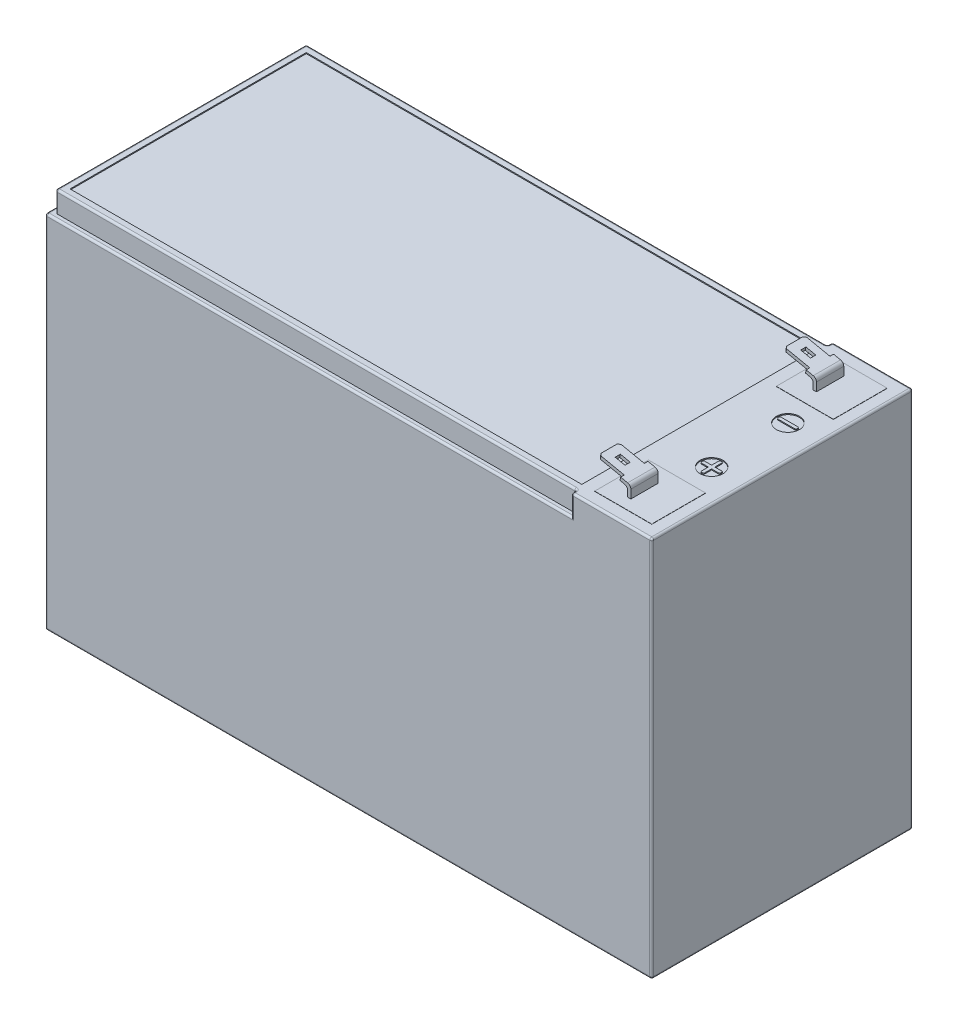
SolidWorks part; units mm, degrees
ref_plane "Front Plane" through (0, 0, 0) normal (0, 0, 1) x (1, 0, 0)
ref_plane "Top Plane" through (0, 0, 0) normal (0, 1, 0) x (1, 0, 0)
ref_plane "Right Plane" through (0, 0, 0) normal (1, 0, 0) x (0, 0, -1)
sketch "Sketch1" plane through (0, 0, 0) normal (0, 1, 0) x (1, 0, 0)
  line L1 (-75.0564, 43.5611) -> (75.9436, 43.5611)
  line L2 (-75.0564, 43.5611) -> (-75.0564, -21.4389)
  line L3 (-75.0564, -21.4389) -> (75.9436, -21.4389)
  line L4 (75.9436, 43.5611) -> (75.9436, -21.4389)
  dimension "D1" = 151
  dimension "D2" = 65
extrude "Boss-Extrude1" add sketch "Sketch1" along normal blind 95
ref_plane "Plane1" through (0, 0, 15.4389) normal (0, 0, 1) x (1, 0, 0)
sketch "Sketch2" plane through (0, 0, 15.4389) normal (0, 0, 1) x (1, 0, 0)
  line L0 (63.9436, 95) -> (63.9436, 97.3257)
  line L1 (-75.0564, 95) -> (75.9436, 95) construction
  line L2 (63.9436, 97.3257) -> (55.7698, 99.03)
  line L3 (55.7698, 99.03) -> (55.9331, 99.8131)
  line L4 (55.9331, 99.8131) -> (64.7436, 97.9761)
  line L5 (64.7436, 97.9761) -> (64.7436, 95)
  line L6 (64.7436, 95) -> (63.9436, 95)
  line L7 (75.9436, 95) -> (75.9436, 0) construction
  point P10 (0, 0)
  dimension "D1" = 12
  dimension "D2" = 9
  dimension "D3" = 0.8
  dimension "D4" = 0.8
extrude "Boss-Extrude2" add sketch "Sketch2" against normal blind 6.8
ref_plane "Plane2" through (0, 0, -11.0611) normal (0, 0, 1) x (1, 0, 0)
sketch "Sketch4" plane through (22.274, 106.8309, 0) normal (0.2041, 0.9789, 0) x (0.9789, -0.2041, 0)
  line L0 (40.7829, -8.6389) -> (40.7829, -9.5389)
  line L1 (43.3829, -8.6389) -> (34.3829, -8.6389) construction
  line L2 (40.7829, -9.5389) -> (34.3829, -9.5389)
  line L3 (34.3829, -8.6389) -> (34.3829, -15.4389) construction
  line L4 (34.3829, -9.5389) -> (34.3829, -8.6389)
  line L5 (34.3829, -8.6389) -> (40.7829, -8.6389)
  line L6 (40.7829, -14.5389) -> (40.7829, -15.4389)
  line L7 (-52.25, -15.4389) -> (52.25, -15.4389) construction
  line L8 (40.7829, -14.5389) -> (34.3829, -14.5389)
  line L9 (34.3829, -14.5389) -> (34.3829, -15.4389)
  line L10 (34.3829, -15.4389) -> (40.7829, -15.4389)
  line L12 (36.5829, -11.3889) -> (39.0829, -11.3889)
  line L13 (36.5829, -11.3889) -> (36.5829, -12.6889)
  line L14 (36.5829, -12.6889) -> (39.0829, -12.6889)
  line L15 (39.0829, -11.3889) -> (39.0829, -12.6889)
  dimension "D1" = 0.9
  dimension "D2" = 0.9
  dimension "D3" = 6.4
  dimension "D4" = 2.2
  dimension "D5" = 2.5
  dimension "D6" = 1.3
  dimension "D7" = 1.85
  dimension "D8" = 1.85
extrude "Cut-Extrude1" cut sketch "Sketch4" against normal up to next (0.8 mm away)
chamfer "Chamfer1" distance 0.5 angle 45 2 edges at (55.8514, 99.4215, 9.5389) (55.8514, 99.4215, 14.5389)
fillet "Fillet1" radius 1 2 edges at (63.9436, 97.3257, 12.0389) (64.7436, 97.9761, 12.0389)
mirror "Mirror1" about plane through (0, 0, -11.0611) normal (0, 0, 1) of "Fillet1", "Chamfer1", "Cut-Extrude1", "Boss-Extrude2"
sketch "Sketch5" plane through (0, 95, 0) normal (0, 1, 0) x (1, 0, 0)
  line L0 (55.9436, -21.4389) -> (55.9436, -20.1389)
  line L1 (-75.0564, -21.4389) -> (75.9436, -21.4389) construction
  line L2 (55.9436, -20.1389) -> (-73.7564, -20.1389)
  line L3 (-73.7564, -20.1389) -> (-73.7564, 42.2611)
  line L4 (-73.7564, 42.2611) -> (55.9436, 42.2611)
  line L5 (55.9436, 42.2611) -> (55.9436, 43.5611)
  line L6 (75.9436, 43.5611) -> (-75.0564, 43.5611) construction
  line L7 (55.9436, 43.5611) -> (-75.0564, 43.5611)
  line L8 (-75.0564, 43.5611) -> (-75.0564, -21.4389)
  line L9 (-75.0564, -21.4389) -> (55.9436, -21.4389)
  line L10 (75.9436, -21.4389) -> (75.9436, 43.5611) construction
  dimension "D1" = 1.3
  dimension "D2" = 1.3
  dimension "D3" = 1.3
  dimension "D4" = 20
  dimension "D5" = 20
extrude "Cut-Extrude2" cut sketch "Sketch5" against normal blind 5.2
fillet "Fillet2" radius 0.5 25 edges at (0.4436, 0, -43.5611) (-75.0564, 44.9, -43.5611) (-75.0564, 0, -11.0611) (-75.0564, 44.9, 21.4389) (75.9436, 0, -11.0611) (0.4436, 0, 21.4389) (75.9436, 47.5, -43.5611) (65.9436, 95, -43.5611) (55.9436, 92.4, -43.5611) (55.9436, 92.4, -42.2611) (55.9436, 95, -42.9111) (-9.5564, 89.8, -43.5611) (-8.9064, 95, -42.2611) (-73.7564, 92.4, -42.2611) (-73.7564, 92.4, 20.1389) (-75.0564, 89.8, -11.0611) (55.9436, 92.4, 20.1389) (-9.5564, 89.8, 21.4389) (55.9436, 92.4, 21.4389) (75.9436, 47.5, 21.4389) (75.9436, 95, -11.0611) (65.9436, 95, 21.4389) (55.9436, 95, 20.7889) (-8.9064, 95, 20.1389) (-73.7564, 95, -11.0611)
sketch "Sketch6" plane through (0, 95, 0) normal (0, 1, 0) x (1, 0, 0)
  line L0 (-73.7564, -19.6389) -> (-73.7564, 41.7611) construction
  line L1 (-71.9564, 40.4611) -> (55.4436, 40.4611)
  line L2 (-71.9564, 40.4611) -> (-71.9564, -18.3389)
  line L3 (-71.9564, -18.3389) -> (55.4436, -18.3389)
  line L4 (55.4436, 40.4611) -> (55.4436, -18.3389)
  line L5 (-73.2564, 42.2611) -> (55.4436, 42.2611) construction
  line L6 (55.4436, -20.1389) -> (-73.2564, -20.1389) construction
  line L7 (75.9436, 43.0611) -> (75.9436, -20.9389) construction
  line L8 (56.4436, 43.5611) -> (75.4436, 43.5611) construction
  line L9 (75.4436, -21.4389) -> (56.4436, -21.4389) construction
  line L10 (67.4436, 3.7111) -> (67.4436, 1.9611)
  line L11 (65.6936, 20.9611) -> (69.9936, 20.9611)
  line L12 (65.4436, 20.7111) -> (65.4436, 20.4111)
  line L13 (65.6936, 20.1611) -> (69.9936, 20.1611)
  line L14 (70.2436, 20.7111) -> (70.2436, 20.4111)
  line L15 (67.4436, 1.9611) -> (65.6936, 1.9611)
  line L16 (65.4436, 1.7111) -> (65.4436, 1.4111)
  line L17 (65.6936, 1.1611) -> (67.4436, 1.1611)
  line L18 (67.4436, 1.1611) -> (67.4436, -0.5889)
  line L19 (67.6936, -0.8389) -> (67.9936, -0.8389)
  line L20 (68.2436, -0.5889) -> (68.2436, 1.1611)
  line L21 (68.2436, 1.1611) -> (69.9936, 1.1611)
  line L22 (70.2436, 1.4111) -> (70.2436, 1.7111)
  line L23 (69.9936, 1.9611) -> (68.2436, 1.9611)
  line L24 (68.2436, 1.9611) -> (68.2436, 3.7111)
  line L25 (67.9936, 3.9611) -> (67.6936, 3.9611)
  line L27 (72.7436, 40.3611) -> (58.5436, 40.3611)
  line L28 (72.7436, 40.3611) -> (72.7436, 26.9611)
  line L29 (72.7436, 26.9611) -> (58.5436, 26.9611)
  line L30 (58.5436, 40.3611) -> (58.5436, 26.9611)
  line L31 (72.7436, -18.2389) -> (58.5436, -18.2389)
  line L32 (72.7436, -18.2389) -> (72.7436, -4.8389)
  line L33 (72.7436, -4.8389) -> (58.5436, -4.8389)
  line L34 (58.5436, -18.2389) -> (58.5436, -4.8389)
  circle A0 centre (67.8436, 20.5611) radius 2.875
  circle A1 centre (67.8436, 1.5611) radius 2.875
  arc A2 (69.9936, 20.1611) -> (70.2436, 20.4111) centre (69.9936, 20.4111) ccw
  arc A3 (70.2436, 20.7111) -> (69.9936, 20.9611) centre (69.9936, 20.7111) ccw
  arc A4 (65.6936, 20.1611) -> (65.4436, 20.4111) centre (65.6936, 20.4111) cw
  arc A5 (65.6936, 20.9611) -> (65.4436, 20.7111) centre (65.6936, 20.7111) ccw
  arc A6 (65.6936, 1.1611) -> (65.4436, 1.4111) centre (65.6936, 1.4111) cw
  arc A7 (65.4436, 1.7111) -> (65.6936, 1.9611) centre (65.6936, 1.7111) cw
  arc A8 (67.6936, -0.8389) -> (67.4436, -0.5889) centre (67.6936, -0.5889) cw
  arc A9 (67.9936, -0.8389) -> (68.2436, -0.5889) centre (67.9936, -0.5889) ccw
  arc A10 (69.9936, 1.1611) -> (70.2436, 1.4111) centre (69.9936, 1.4111) ccw
  arc A11 (70.2436, 1.7111) -> (69.9936, 1.9611) centre (69.9936, 1.7111) ccw
  arc A12 (68.2436, 3.7111) -> (67.9936, 3.9611) centre (67.9936, 3.7111) ccw
  arc A13 (67.6936, 3.9611) -> (67.4436, 3.7111) centre (67.6936, 3.7111) ccw
  dimension "D5" = 5.75
  dimension "D8" = 5.75
  dimension "D27" = 0.25
  dimension "D1" = 1.8
  dimension "D2" = 1.8
  dimension "D3" = 1.8
  dimension "D4" = 20.5
  dimension "D6" = 8.1
  dimension "D7" = 23
  dimension "D9" = 8.1
  dimension "D10" = 23
  dimension "D11" = 0.4
  dimension "D12" = 0.4
  dimension "D13" = 2.4
  dimension "D14" = 2.4
  dimension "D15" = 0.4
  dimension "D16" = 0.4
  dimension "D17" = 0.4
  dimension "D18" = 0.4
  dimension "D19" = 0.4
  dimension "D20" = 0.4
  dimension "D21" = 0.4
  dimension "D22" = 0.4
  dimension "D23" = 2.4
  dimension "D24" = 2.4
  dimension "D25" = 2.4
  dimension "D26" = 2.4
  dimension "D28" = 3.2
  dimension "D29" = 3.2
  dimension "D30" = 14.2
  dimension "D31" = 13.4
  dimension "D32" = 3.2
  dimension "D33" = 3.2
  dimension "D34" = 14.2
  dimension "D35" = 13.4
extrude "Cut-Extrude3" cut sketch "Sketch6" against normal blind 0.25
sketch "Sketch7" plane through (0, 94.75, 0) normal (0, 1, 0) x (1, 0, 0)
  line L0 (58.5436, 26.9611) -> (72.7436, 26.9611) construction
  line L1 (72.7436, 26.9611) -> (72.7436, 40.3611) construction
  line L2 (58.5436, 40.3611) -> (58.5436, 26.9611) construction
  line L3 (72.7436, 40.3611) -> (58.5436, 40.3611) construction
  line L4 (58.5436, 26.9611) -> (72.7436, 26.9611)
  line L5 (72.7436, 26.9611) -> (72.7436, 40.3611)
  line L6 (58.5436, 40.3611) -> (58.5436, 26.9611)
  line L7 (72.7436, 40.3611) -> (58.5436, 40.3611)
extrude "Boss-Extrude3" add sketch "Sketch7" along normal blind 0.3
sketch "Sketch8" plane through (0, 94.75, 0) normal (0, 1, 0) x (1, 0, 0)
  line L0 (58.5436, -18.2389) -> (72.7436, -18.2389) construction
  line L1 (72.7436, -18.2389) -> (72.7436, -4.8389) construction
  line L2 (58.5436, -4.8389) -> (58.5436, -18.2389) construction
  line L3 (72.7436, -4.8389) -> (58.5436, -4.8389) construction
  line L4 (58.5436, -18.2389) -> (72.7436, -18.2389)
  line L5 (72.7436, -18.2389) -> (72.7436, -4.8389)
  line L6 (58.5436, -4.8389) -> (58.5436, -18.2389)
  line L7 (72.7436, -4.8389) -> (58.5436, -4.8389)
extrude "Boss-Extrude4" add sketch "Sketch8" along normal blind 0.3
ref_plane "Plane3" through (0.4436, 0, 0) normal (-1, 0, 0) x (0, 0, 1)
sketch "Sketch9" plane through (0, 0, 0) normal (0, -1, 0) x (1, 0, 0)
  line L0 (-70.0564, 8.7389) -> (-70.0564, 15.9389)
  line L1 (-69.5564, 16.4389) -> (-62.3564, 16.4389)
  line L2 (-61.8564, 15.9389) -> (-61.8564, 14.9389)
  line L3 (-62.3564, 14.4389) -> (-68.0564, 14.4389)
  line L4 (-68.0564, 14.4389) -> (-68.0564, 8.7389)
  line L5 (-68.5564, 8.2389) -> (-69.5564, 8.2389)
  line L6 (-74.5564, 21.4389) -> (75.4436, 21.4389) construction
  line L7 (-75.0564, -43.0611) -> (-75.0564, 20.9389) construction
  arc A0 (-68.5564, 8.2389) -> (-68.0564, 8.7389) centre (-68.5564, 8.7389) ccw
  arc A1 (-69.5564, 8.2389) -> (-70.0564, 8.7389) centre (-69.5564, 8.7389) cw
  arc A2 (-62.3564, 14.4389) -> (-61.8564, 14.9389) centre (-62.3564, 14.9389) ccw
  arc A3 (-61.8564, 15.9389) -> (-62.3564, 16.4389) centre (-62.3564, 15.9389) ccw
  arc A4 (-69.5564, 16.4389) -> (-70.0564, 15.9389) centre (-69.5564, 15.9389) ccw
  dimension "D7" = 0.5
  dimension "D1" = 8.2
  dimension "D2" = 8.2
  dimension "D3" = 2
  dimension "D4" = 2
  dimension "D5" = 5
  dimension "D6" = 5
extrude "Boss-Extrude5" add sketch "Sketch9" along normal blind 0.5
mirror "Mirror2" about plane through (0.4436, 0, 0) normal (-1, 0, 0) of "Boss-Extrude5"
mirror "Mirror3" about plane through (0, 0, -11.0611) normal (0, 0, 1) of "Mirror2", "Boss-Extrude5"
